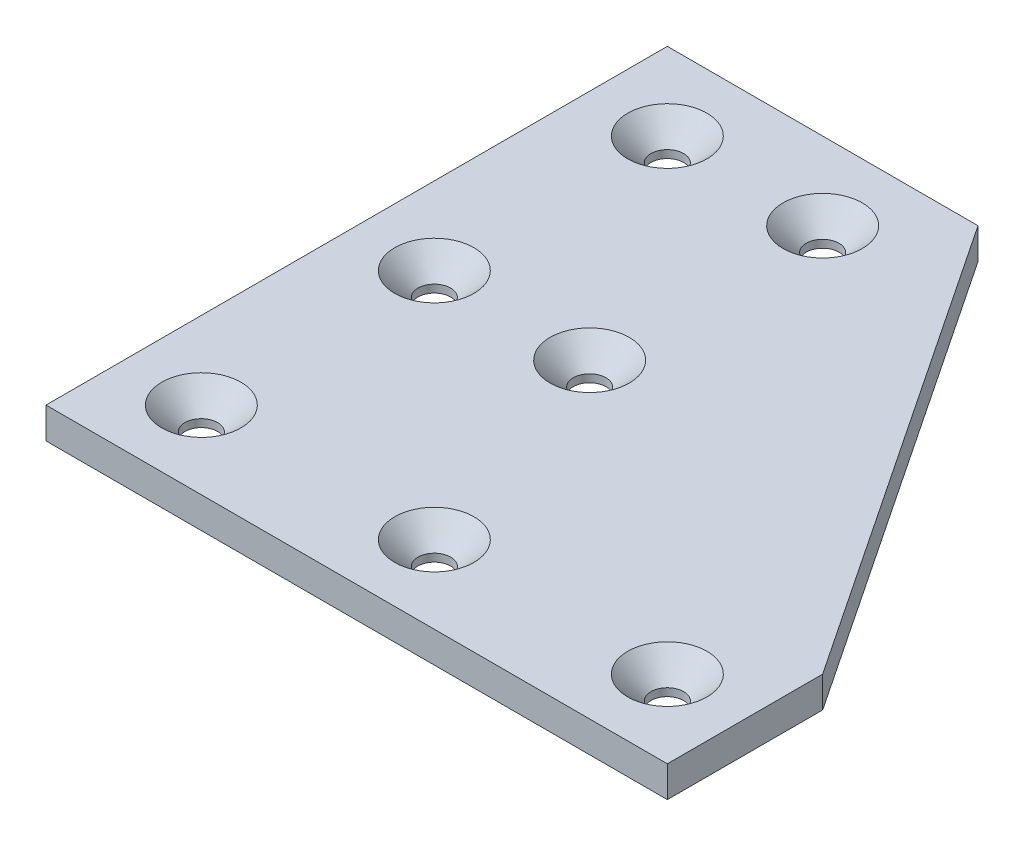
SolidWorks part; units mm, degrees
material "1060 Alloy"
ref_plane "Front Plane" through (0, 0, 0) normal (0, 0, 1) x (1, 0, 0)
ref_plane "Top Plane" through (0, 0, 0) normal (0, 1, 0) x (1, 0, 0)
ref_plane "Right Plane" through (0, 0, 0) normal (1, 0, 0) x (0, 0, -1)
sketch "Sketch1" plane through (0, 0, 0) normal (0, 1, 0) x (1, 0, 0)
  line L0 (0, 0) -> (80, 0)
  line L1 (80, 0) -> (80, 20)
  line L2 (80, 20) -> (40, 80)
  line L3 (40, 80) -> (0, 80)
  line L4 (0, 80) -> (0, 0)
  point P0 (40.0308, 79.9539)
  point P1 (0, 0)
  point P8 (0, 80)
  point P11 (40, 80)
  point P14 (80, 20)
  point P17 (80, 0)
  point P20 (0, 0)
  dimension "D1" = 80
  dimension "D2" = 80
  dimension "D3" = 20
  dimension "D4" = 40
extrude "Boss-Extrude1" add sketch "Sketch1" along normal blind 4
sketch "Sketch2" plane through (0, 4, 0) normal (0, 1, 0) x (1, 0, 0)
  line L0 (0, 0) -> (80, 0) construction
  line L1 (0, 80) -> (0, 0) construction
  line L2 (80, 0) -> (80, 20) construction
  line L3 (40, 80) -> (0, 80) construction
  circle A0 centre (10, 10) radius 2.1
  circle A1 centre (40, 10) radius 2.1
  circle A2 centre (70, 10) radius 2.1
  circle A4 centre (30, 40) radius 2.1
  circle A5 centre (30, 70) radius 2.1
  circle A6 centre (10, 40) radius 2.1
  circle A7 centre (10, 70) radius 2.1
  circle A8 centre (30, 10) radius 2.1 [skipped]
  dimension "D1" = 4.2
  dimension "D3" = 3
  dimension "D2" = 10
  dimension "10" = 10
  dimension "D4" = 10
  dimension "D7" = 10
  dimension "D8" = 10
  dimension "D9" = 20
  dimension "D5" = 2
  dimension "D6" = 3
extrude "Cut-Extrude1" cut sketch "Sketch2" against normal blind 4
chamfer "Chamfer1" distance 3 angle 45 7 edges at (70, 4, -7.9) (40, 4, -7.9) (10, 4, -7.9) (30, 4, -37.9) (10, 4, -37.9) (30, 4, -67.9) (10, 4, -67.9)
fillet "Fillet1" [suppressed] radius 1
